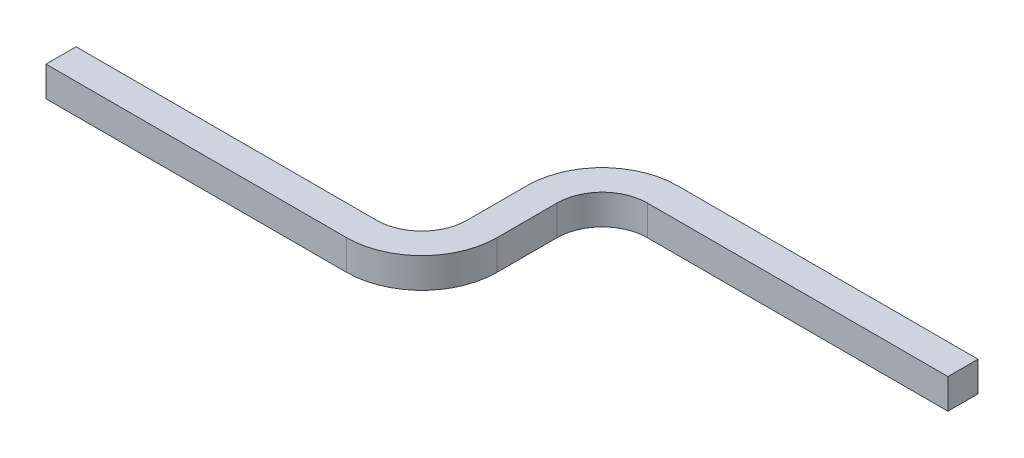
SolidWorks part; units mm, degrees
ref_plane "Front Plane" through (0, 0, 0) normal (0, 0, 1) x (1, 0, 0)
ref_plane "Top Plane" through (0, 0, 0) normal (0, 1, 0) x (1, 0, 0)
ref_plane "Right Plane" through (0, 0, 0) normal (1, 0, 0) x (0, 0, -1)
sketch "Sketch1" plane through (0, 0, 0) normal (0, 1, 0) x (1, 0, 0)
  line L0 (0, 0) -> (100, 0)
  line L1 (120, 20) -> (120, 40)
  line L2 (140, 60) -> (240, 60)
  arc A0 (100, 0) -> (120, 20) centre (100, 20) ccw
  arc A1 (120, 40) -> (140, 60) centre (140, 40) cw
  dimension "D2" = 20
  dimension "D4" = 20
  dimension "D1" = 100
  dimension "D3" = 20
  dimension "D5" = 100
sketch "Sketch3" plane through (0, 0, 0) normal (1, 0, 0) x (0, 0, -1)
  line L1 (5, -5) -> (-5, -5)
  line L2 (5, -5) -> (5, 5)
  line L3 (5, 5) -> (-5, 5)
  line L4 (-5, -5) -> (-5, 5)
  line L5 (5, -5) -> (-5, 5) construction
  line L6 (5, 5) -> (-5, -5) construction
  point P0 (0, 0)
  dimension "D1" = 10
  dimension "D2" = 10
sweep "Sweep3" add profiles "Sketch3" path "Sketch1"
